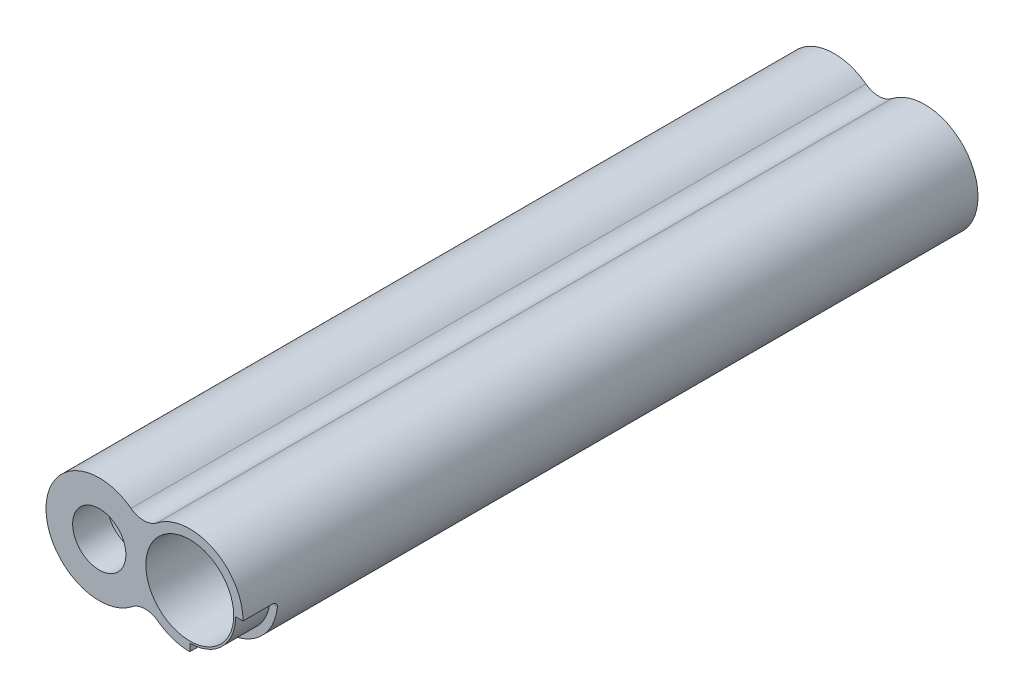
SolidWorks part; units mm, degrees
material "PVC 0.007 Plasticized"
ref_plane "Front Plane" through (0, 0, 0) normal (0, 0, 1) x (1, 0, 0)
ref_plane "Top Plane" through (0, 0, 0) normal (0, 1, 0) x (1, 0, 0)
ref_plane "Right Plane" through (0, 0, 0) normal (1, 0, 0) x (0, 0, -1)
sketch "Sketch1" plane through (0, 0, 0) normal (0, 0, 1) x (1, 0, 0)
  line L0 (-5, 9.1089) -> (13.5, 9.1089) construction
  line L1 (-5, 9.1089) -> (-5, -6.9128) construction
  line L2 (13.5, 9.1089) -> (13.5, -9.8935) construction
  arc A0 (2.9861, 4.0104) -> (3.0853, -3.9346) centre (0, 0) ccw
  arc A1 (5.5139, -3.9043) -> (5.4147, 4.0407) centre (8.5, 0.1061) ccw
  arc A2 (5.4147, 4.0407) -> (2.9861, 4.0104) centre (4.1806, 5.6145) cw
  arc A3 (5.5139, -3.9043) -> (3.0853, -3.9346) centre (4.3194, -5.5084) ccw
  circle A4 centre (0, 0) radius 4.125
  circle A5 centre (8.5, 0.1061) radius 4.125
  dimension "D1" = 10
  dimension "D3" = 2
  dimension "D4" = 2
  dimension "D5" = 8.25
  dimension "D2" = 18.5
extrude "Boss-Extrude1" add sketch "Sketch1" along normal mid plane 69 contours A1 A2 A0 A3
sketch "Sketch2" plane through (0, 0, 0) normal (0, 0, 1) x (1, 0, 0)
  circle A0 centre (0, 0) radius 4.125
  circle A1 centre (8.5, 0.1061) radius 4.125
  dimension "D1" = 8.25
extrude "Cut-Extrude1" cut sketch "Sketch2" against normal mid plane 69
sketch "Sketch3" plane through (0, 0, 34.5) normal (0, 0, 1) x (1, 0, 0)
  circle A0 centre (0, 0) radius 4.125
  circle A1 centre (0, 0) radius 2.5
  dimension "D1" = 5
extrude "Boss-Extrude2" add sketch "Sketch3" against normal blind 3.25
sketch "Sketch5" plane through (0, 0, -34.5) normal (0, 0, -1) x (-1, 0, 0)
  circle A0 centre (-8.5, 0.1061) radius 4.125 construction
  circle A1 centre (-8.5, 0.1061) radius 4.125
  circle A2 centre (-8.5, 0.1061) radius 2.5
  dimension "D1" = 5
extrude "Boss-Extrude4" add sketch "Sketch5" against normal blind 3.25
sketch "Sketch6" plane through (0, 0, -34.5) normal (0, 0, -1) x (-1, 0, 0)
  line L0 (4.2996, -0.0624) -> (4.9996, -0.0624)
  line L1 (0, -4.3001) -> (0, -5)
  arc A0 (-3.0853, -3.9346) -> (-2.9861, 4.0104) centre (0, 0) ccw construction
  arc A1 (0, -4.3001) -> (4.2996, -0.0624) centre (0, 0) ccw
  arc A2 (0, -5) -> (4.9996, -0.0624) centre (0, 0) ccw
  dimension "D1" = 0.7
extrude "Cut-Extrude3" cut sketch "Sketch6" against normal blind 3.25 contours A2 L0 A1 L1
fillet "Fillet1" radius 0.5 2 edges at (0, -4.65, -31.25) (-4.6496, -0.0624, -31.25)
sketch "Sketch7" plane through (0, 0, 34.5) normal (0, 0, 1) x (1, 0, 0)
  line L0 (13.5, 0.1061) -> (12.8, 0.1061)
  line L1 (8.5, -4.8939) -> (8.5, -4.1939)
  arc A0 (8.5, -4.8939) -> (13.5, 0.1061) centre (8.5, 0.1061) ccw
  arc A2 (5.5139, -3.9043) -> (5.4147, 4.0407) centre (8.5, 0.1061) ccw construction
  arc A3 (8.5, -4.1939) -> (12.8, 0.1061) centre (8.5, 0.1061) ccw
  dimension "D2" = 0.7
extrude "Cut-Extrude4" cut sketch "Sketch7" against normal blind 3.25
fillet "Fillet2" radius 0.5 2 edges at (8.5, -4.5439, 31.25) (13.15, 0.1061, 31.25)
